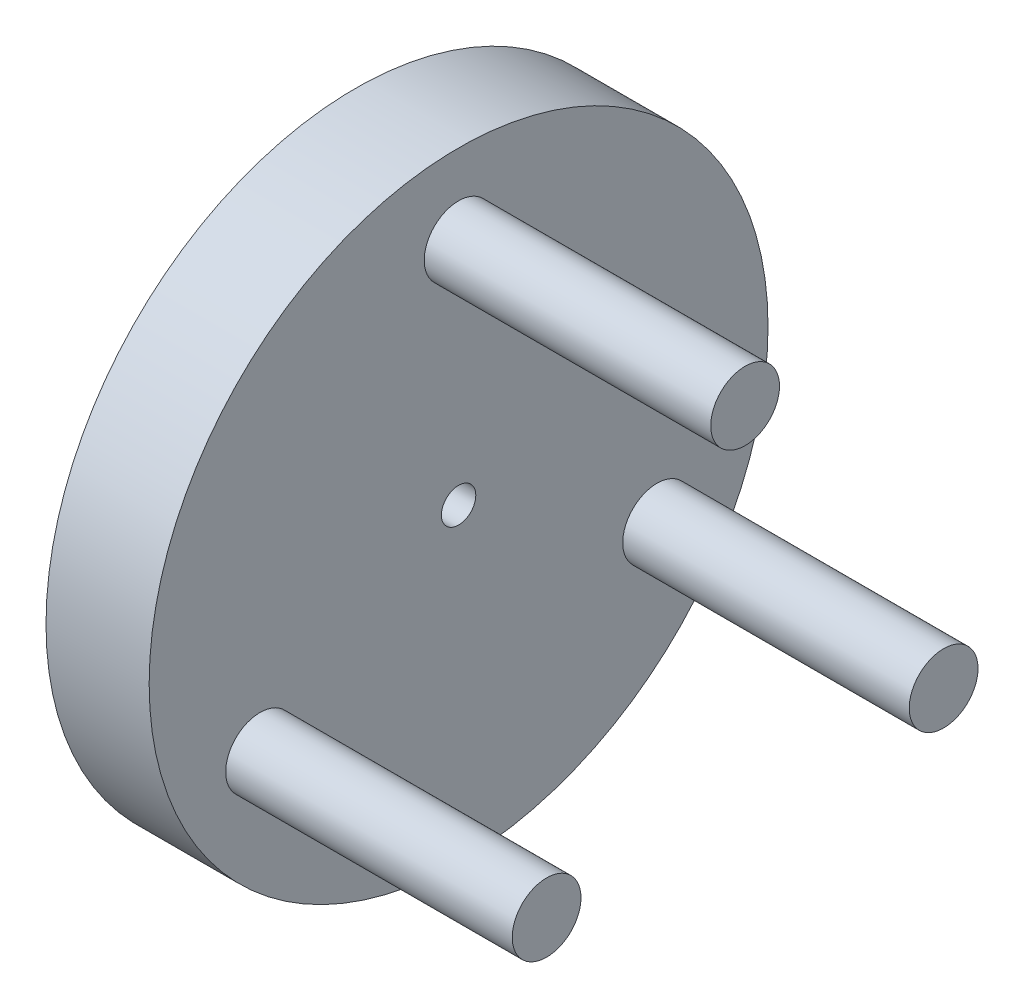
SolidWorks part; units mm, degrees
ref_plane "Front Plane" through (0, 0, 0) normal (0, 0, 1) x (1, 0, 0)
ref_plane "Top Plane" through (0, 0, 0) normal (0, 1, 0) x (1, 0, 0)
ref_plane "Right Plane" through (0, 0, 0) normal (1, 0, 0) x (0, 0, -1)
sketch "Sketch1" plane through (0, 0, 0) normal (1, 0, 0) x (0, 0, -1)
  circle A0 centre (0, 0) radius 1.25
  circle A1 centre (0, 0) radius 2.8
  circle A2 centre (0, 0) radius 27
  dimension "D1" = 2.5
  dimension "D2" = 5.6
  dimension "D3" = 54
extrude "Boss-Extrude2" add sketch "Sketch1" along normal blind 4 contours A2 A1
sketch "Sketch2" plane through (4, 0, 0) normal (1, 0, 0) x (0, 0, -1)
  circle A0 centre (0, 0) radius 2.8
  circle A1 centre (0, 0) radius 1.5
  circle A2 centre (0, 0) radius 36
  circle M1 centre (0, 0) radius 2.8
  circle M2 centre (0, 0) radius 27
  dimension "D1" = 3
  dimension "D2" = 5.6
  dimension "D3" = 72
extrude "Boss-Extrude3" add sketch "Sketch2" along normal blind 5 contours M2 M1 | A1 M1
ref_plane "Plane4" through (9, 0, 0) normal (1, 0, 0) x (0, 0, -1)
sketch "Sketch3" plane through (9, 0, 0) normal (1, 0, 0) x (0, 0, -1)
  circle A4 centre (0, 20) radius 3
  circle A5 centre (17.3205, -10) radius 3
  circle A6 centre (-17.3205, -10) radius 3
  point P14 (0, 0)
  dimension "D1" = 3
  dimension "D2" = 6
extrude "Boss-Extrude4" add sketch "Sketch3" along normal blind 25
ref_plane "Plane5" through (29, 0, 0) normal (1, 0, 0) x (0, 0, -1)
sketch "Sketch4" plane through (9, 0, 0) normal (1, 0, 0) x (0, 0, -1)
  circle A0 centre (0, 0) radius 12.2
  circle A1 centre (0, 0) radius 7.64
  dimension "D1" = 24.4
  dimension "D2" = 15.28
extrude "Boss-Extrude5" add sketch "Sketch4" along normal blind 3
sketch "Sketch5" plane through (12, 0, 0) normal (1, 0, 0) x (0, 0, -1)
  circle A0 centre (0, 0) radius 7.64
  circle A1 centre (0, 0) radius 12.2
extrude "Cut-Extrude1" cut sketch "Sketch5" against normal blind 3
